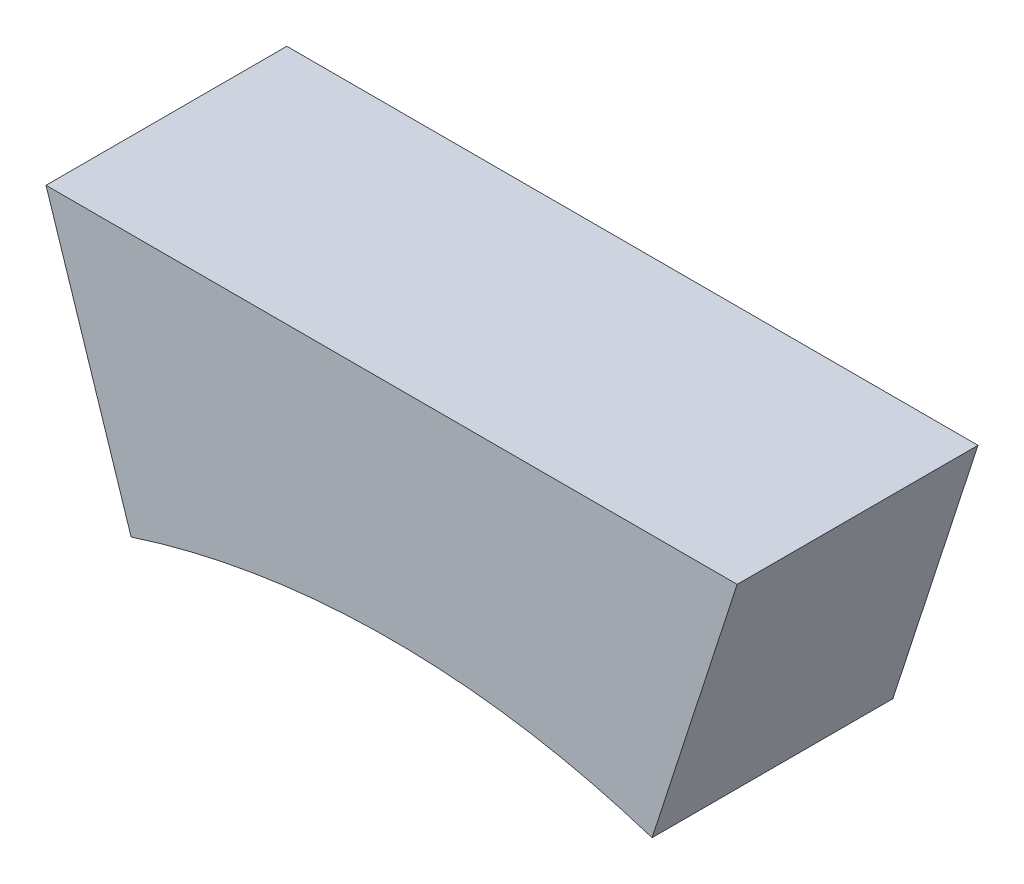
SolidWorks part; units mm, degrees
material "砖"
ref_plane "前视基准面" through (0, 0, 0) normal (0, 0, 1) x (1, 0, 0)
ref_plane "上视基准面" through (0, 0, 0) normal (0, 1, 0) x (1, 0, 0)
ref_plane "右视基准面" through (0, 0, 0) normal (1, 0, 0) x (0, 0, -1)
sketch "草图1" plane through (0, 0, 0) normal (0, 0, 1) x (1, 0, 0)
  line L0 (-4560, 0) -> (-7920, 0)
  line L1 (-12480, 7680) -> (0, 7680)
  line L2 (-12480, 7680) -> (-12480, 0)
  line L3 (-12480, 0) -> (0, 0)
  line L4 (0, 7680) -> (0, 0)
  line L5 (-7920, 0) -> (-7920, 3840)
  line L6 (-7920, 3840) -> (-4560, 3840)
  line L7 (-4560, 3840) -> (-4560, 0)
  line L8 (-7920, 3840) -> (-8160, 3840)
  line L9 (-4560, 3840) -> (-4320, 3840)
  line L10 (-7837.7749, 4359.1486) -> (-8066.0285, 4433.3126)
  line L11 (-7599.1486, 4827.4792) -> (-7793.3126, 4968.5477)
  line L12 (-7227.4792, 5199.1486) -> (-7368.5477, 5393.3126)
  line L13 (-6759.1486, 5437.7749) -> (-6833.3126, 5666.0285)
  line L14 (-6240, 5520) -> (-6240, 5760)
  line L15 (-5720.8514, 5437.7749) -> (-5646.6874, 5666.0285)
  line L16 (-5252.5208, 5199.1486) -> (-5111.4523, 5393.3126)
  line L17 (-4880.8514, 4827.4792) -> (-4686.6874, 4968.5477)
  line L18 (-4642.2251, 4359.1486) -> (-4413.9715, 4433.3126)
  line L19 (-4560, 3840) -> (-4320, 3840)
  line L20 (-4573.7633, 3298.6069) -> (-4560, 3294.1349)
  line L21 (-6833.3126, 5666.0285) -> (-6928.8298, 5960)
  line L22 (-5683.7694, 5551.9017) -> (-5551.1702, 5960)
  line L23 (-5551.1702, 5960) -> (-6928.8298, 5960)
  line L24 (-7920, 0) -> (-9123.3069, 0)
  line L25 (-8160, 0) -> (-8640, 0)
  line L26 (-8160, 0) -> (-8640, 0)
  line L27 (-8640, 3840) -> (-8160, 3840)
  line L28 (-8640, 3840) -> (-8640, 4264)
  line L29 (-7837.7749, 3320.8514) -> (-7920, 3294.1349) [skipped]
  line L30 (-7599.1486, 2852.5208) -> (-7793.3126, 2711.4523) [skipped]
  line L31 (-7227.4792, 2480.8514) -> (-7368.5477, 2286.6874) [skipped]
  line L32 (-6759.1486, 2242.2251) -> (-6833.3126, 2013.9715) [skipped]
  line L33 (-6240, 2160) -> (-6240, 1920) [skipped]
  line L34 (-5720.8514, 2242.2251) -> (-5646.6874, 2013.9715) [skipped]
  line L35 (-5252.5208, 2480.8514) -> (-5111.4523, 2286.6874) [skipped]
  line L36 (-4880.8514, 2852.5208) -> (-4686.6874, 2711.4523) [skipped]
  line L37 (-8640, 4264) -> (-8112.5982, 4264)
  line L38 (-8112.5982, 4264) -> (-8592.5982, 4264)
  line L39 (-8592.5982, 4264) -> (-8592.5982, 4688)
  line L40 (-8592.5982, 4688) -> (-7962.5841, 4688)
  line L41 (-7962.5841, 4688) -> (-8442.5841, 4688)
  line L42 (-8442.5841, 4688) -> (-8442.5841, 5112)
  line L43 (-8442.5841, 5112) -> (-7678.1989, 5112)
  line L44 (-7678.1989, 5112) -> (-8158.1989, 5112)
  line L45 (-8158.1989, 5112) -> (-8158.1989, 5536)
  line L46 (-8158.1989, 5536) -> (-7139.9911, 5536)
  line L47 (-7139.9911, 5536) -> (-7619.9911, 5536)
  line L48 (-7619.9911, 5536) -> (-7619.9911, 5960)
  line L49 (-7619.9911, 5960) -> (-6928.8298, 5960)
  arc A0 (-4560, 3840) -> (-7920, 3840) centre (-6240, 3840) ccw
  arc A1 (-4320, 3840) -> (-8160, 3840) centre (-6240, 3840) ccw
  point P7 (-6240, 0)
  point P56 (-6240, 3840)
  dimension "D5" = 3840
  dimension "D1" = 12480
  dimension "D2" = 7680
  dimension "D3" = 3360
  dimension "D4" = 3840
  dimension "D7" = 240
  dimension "D8" = 480
  dimension "D9" = 424
  dimension "D10" = 720
  dimension "D11" = 480
  dimension "D12" = 480
  dimension "D13" = 480
  dimension "D14" = 480
  dimension "D6" = 20
extrude "凸台-拉伸1" add sketch "草图1" along normal blind 480 contours L14 A1 L13 A0 | L15 A1 L14 A0 | A1 L22 L23 L21
scale "缩放比例1" scale about origin uniform scaling yes scale factor 1.3
